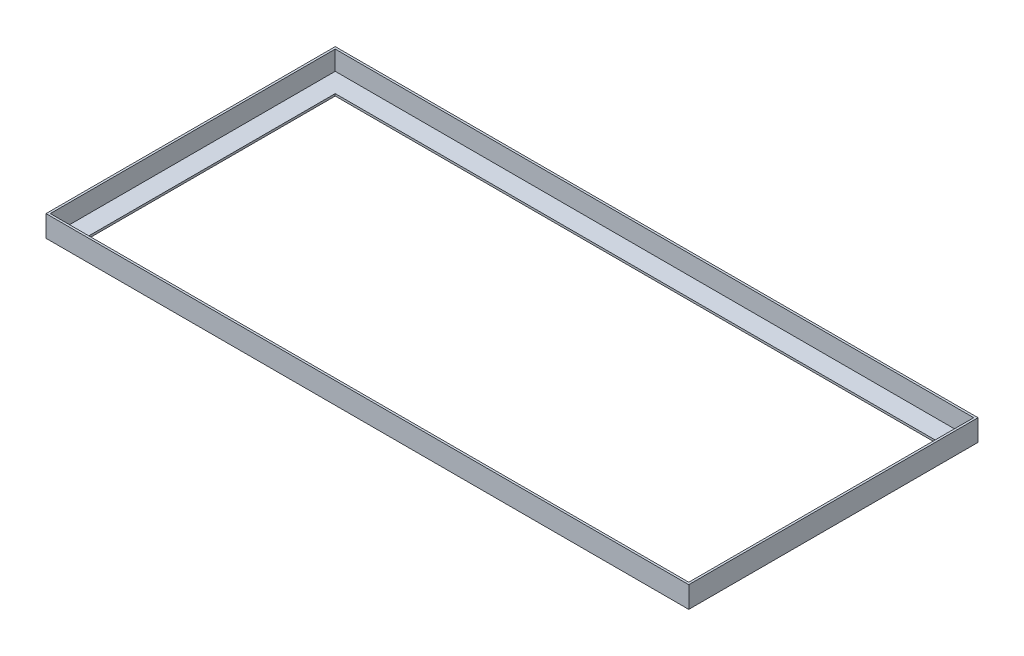
SolidWorks part; units mm, degrees
material "AISI 1020"
ref_plane "Front Plane" through (0, 0, 0) normal (0, 0, 1) x (1, 0, 0)
ref_plane "Top Plane" through (0, 0, 0) normal (0, 1, 0) x (1, 0, 0)
ref_plane "Right Plane" through (0, 0, 0) normal (1, 0, 0) x (0, 0, -1)
sketch "Sketch1" plane through (0, 0, 0) normal (0, 0, 1) x (1, 0, 0)
  line L1 (-78.9001, 15.665) -> (521.0999, 15.665)
  line L2 (-78.9001, 15.665) -> (-78.9001, -4.335)
  line L3 (-78.9001, -4.335) -> (521.0999, -4.335)
  line L4 (521.0999, 15.665) -> (521.0999, -4.335)
  dimension "D1" = 20
  dimension "D2" = 600
extrude "Boss-Extrude1" add sketch "Sketch1" against normal blind 270
sketch3d "3DSketch1"
  line L0 (519.0999, 15.665, -268) -> (-76.9001, 15.665, -268)
  line L1 (-76.9001, 15.665, -268) -> (-76.9001, 15.665, -2)
  line L2 (519.0999, 15.665, -2) -> (-76.9001, 15.665, -2)
  line L3 (519.0999, 15.665, -268) -> (519.0999, 15.665, -2)
  line L4 (519.0999, 15.665, -268) -> (-76.9001, 15.665, -268)
  line L5 (-76.9001, 15.665, -268) -> (-76.9001, 15.665, -2)
  line L6 (519.0999, 15.665, -2) -> (-76.9001, 15.665, -2)
  line L7 (519.0999, 15.665, -268) -> (519.0999, 15.665, -2)
  dimension "D1" = 2
extrude "Cut-Extrude1" cut sketch "3DSketch1" along direction (0, 1, 0) on the side against the normal blind 18
sketch3d "3DSketch2"
  line L0 (-58.9001, -2.335, -250) -> (501.0999, -2.335, -250)
  line L1 (-58.9001, -2.335, -20) -> (-58.9001, -2.335, -250)
  line L2 (501.0999, -2.335, -20) -> (-58.9001, -2.335, -20)
  line L3 (501.0999, -2.335, -250) -> (501.0999, -2.335, -20)
  line L4 (-58.9001, -2.335, -250) -> (501.0999, -2.335, -250)
  line L5 (-58.9001, -2.335, -20) -> (-58.9001, -2.335, -250)
  line L6 (501.0999, -2.335, -20) -> (-58.9001, -2.335, -20)
  line L7 (501.0999, -2.335, -250) -> (501.0999, -2.335, -20)
  dimension "D1" = 18
extrude "Cut-Extrude2" cut sketch "3DSketch2" along direction (0, -1, 0) on the side against the normal blind 2
